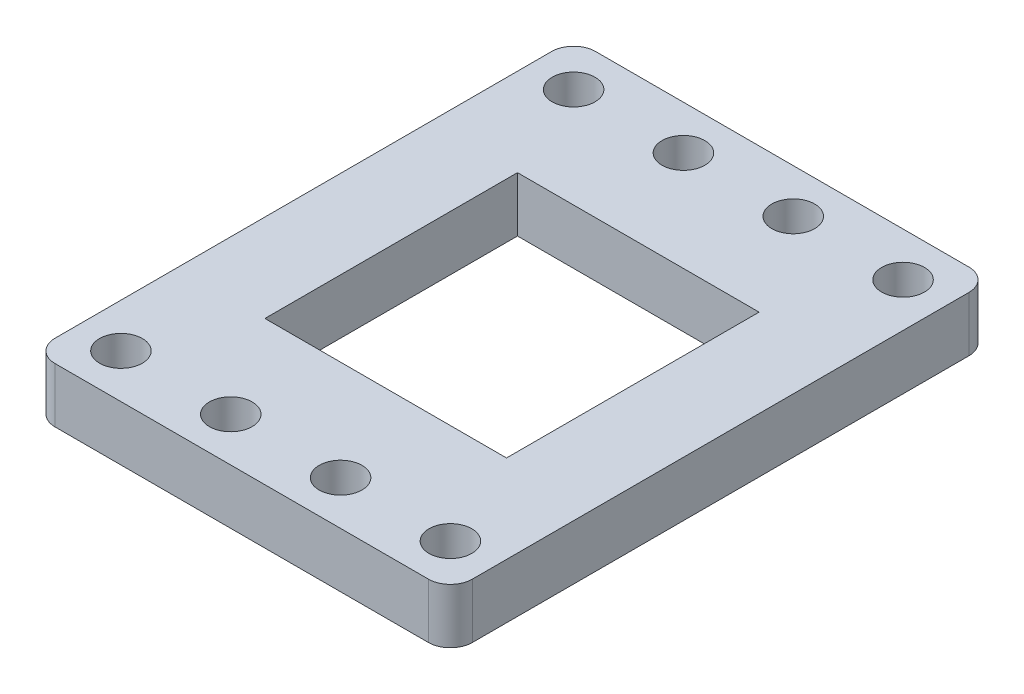
SolidWorks part; units mm, degrees
ref_plane "Front Plane" through (0, 0, 0) normal (0, 0, 1) x (1, 0, 0)
ref_plane "Top Plane" through (0, 0, 0) normal (0, 1, 0) x (1, 0, 0)
ref_plane "Right Plane" through (0, 0, 0) normal (1, 0, 0) x (0, 0, -1)
sketch "Sketch1" plane through (0, 0, 0) normal (0, 1, 0) x (1, 0, 0)
  line L1 (-36, 0) -> (-2, 0)
  line L2 (-38, -2) -> (-38, -47.22)
  line L3 (-36, -49.22) -> (-2, -49.22)
  line L4 (0, -2) -> (0, -47.22)
  arc A0 (-2, -49.22) -> (0, -47.22) centre (-2, -47.22) ccw
  arc A1 (-38, -47.22) -> (-36, -49.22) centre (-36, -47.22) ccw
  arc A2 (-36, 0) -> (-38, -2) centre (-36, -2) ccw
  arc A3 (-2, 0) -> (0, -2) centre (-2, -2) cw
  point P7 (0, -49.22)
  point P12 (-38, 0)
  point P15 (0, 0)
  dimension "D3" = 2
  dimension "D1" = 38
  dimension "D2" = 49.22
extrude "Boss-Extrude1" add sketch "Sketch1" along normal blind 5
sketch "Sketch2" plane through (0, 5, 0) normal (0, 1, 0) x (1, 0, 0)
  line L0 (-2, 0) -> (-36, 0) construction
  line L1 (0, -47.22) -> (0, -2) construction
  line L2 (-4, -4) -> (-54, -4) construction
  line L3 (-19, -13.11) -> (-19, -36.11) construction
  line L4 (-4, -45.22) -> (-54, -45.22) construction
  line L5 (-36, -49.22) -> (-2, -49.22) construction
  line L6 (-30, -24.61) -> (-8, -24.61) construction
  line L7 (-30, -13.11) -> (-8, -13.11)
  line L8 (-30, -13.11) -> (-30, -36.11)
  line L9 (-30, -36.11) -> (-8, -36.11)
  line L10 (-8, -13.11) -> (-8, -36.11)
  line L11 (-38, -2) -> (-38, -47.22) construction
  circle A20 centre (-4, -4) radius 1.95
  circle A21 centre (-14, -4) radius 1.95
  circle A22 centre (-24, -4) radius 1.95
  circle A23 centre (-54, -4) radius 1.95
  circle A24 centre (-34, -4) radius 1.95
  circle A25 centre (-44, -4) radius 1.95
  circle A26 centre (-44, -45.22) radius 1.95
  circle A27 centre (-34, -45.22) radius 1.95
  circle A28 centre (-54, -45.22) radius 1.95
  circle A29 centre (-24, -45.22) radius 1.95
  circle A30 centre (-14, -45.22) radius 1.95
  circle A31 centre (-4, -45.22) radius 1.95
  dimension "D1" = 10
  dimension "D7" = 3.9
  dimension "D8" = 3.9
  dimension "D9" = 3.9
  dimension "D10" = 10
  dimension "D11" = 10
  dimension "D12" = 10
  dimension "D13" = 4
  dimension "D14" = 4
  dimension "D3" = 3.9
  dimension "D5" = 3.9
  dimension "D6" = 3.9
  dimension "D2" = 10
  dimension "D42" = 23
  dimension "D44" = 22
extrude "Cut-Extrude1" cut sketch "Sketch2" against normal through all
